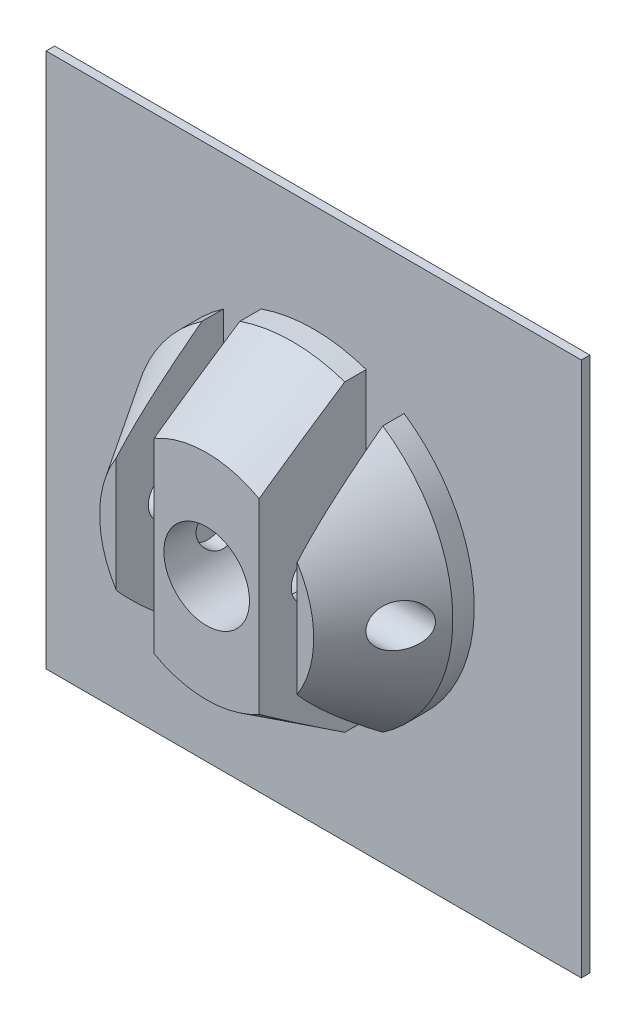
SolidWorks part; units mm, degrees
ref_plane "Alzado" through (0, 0, 0) normal (0, 0, 1) x (1, 0, 0)
ref_plane "Planta" through (0, 0, 0) normal (0, 1, 0) x (1, 0, 0)
ref_plane "Vista lateral" through (0, 0, 0) normal (1, 0, 0) x (0, 0, -1)
sketch "Croquis1" plane through (0, 0, 0) normal (0, 0, 1) x (1, 0, 0)
  line L1 (25, -25) -> (-25, -25)
  line L2 (25, -25) -> (25, 25)
  line L3 (25, 25) -> (-25, 25)
  line L4 (-25, -25) -> (-25, 25)
  line L5 (25, -25) -> (-25, 25) construction
  line L6 (25, 25) -> (-25, -25) construction
  circle A0 centre (0, 0) radius 2
  point P0 (0, 0)
  dimension "D3" = 4
  dimension "D1" = 50
  dimension "D2" = 50
extrude "Saliente-Extruir2" add sketch "Croquis1" along normal blind 0.8
ref_plane "Plano1" through (0, 0, 0) normal (1, 0, 0) x (0, 0, -1)
sketch "Croquis2" plane through (0, 0, 0) normal (1, 0, 0) x (0, 0, -1)
  line L0 (-0.8, 0) -> (-10.8, 0)
  line L1 (-0.8, 25) -> (-0.8, -25) construction
  line L2 (-10.8, 0) -> (-10.8, 10)
  line L3 (-0.8, 15) -> (-2.8, 15)
  line L4 (-0.8, 15) -> (-0.8, 0)
  line L5 (-2.8, 15) -> (-10.8, 10)
  dimension "D1" = 10
  dimension "D2" = 10
  dimension "D3" = 2
  dimension "D4" = 15
revolve "Revolución1" add sketch "Croquis2" angle 360 about L0
sketch "Croquis3" plane through (0, 0, 0.8) normal (0, 0, 1) x (1, 0, 0)
  line L2 (20, -25) -> (25, -25)
  line L3 (25, -25) -> (25, -20)
  arc A1 (20, -25) -> (25, -20) centre (25, -25) ccw
  dimension "D2" = 10
sketch "Croquis4" plane through (0, 0, 10.8) normal (0, 0, 1) x (1, 0, 0)
  line L0 (0, -0.44) -> (0, 0.44) construction
  line L1 (-8.45, 20) -> (-4.9, 20)
  line L2 (-8.45, 20) -> (-8.45, -20)
  line L3 (-8.45, -20) -> (-4.9, -20)
  line L4 (-4.9, 20) -> (-4.9, -20)
  line L5 (8.45, -20) -> (4.9, -20)
  line L6 (4.9, 20) -> (4.9, -20)
  line L7 (8.45, 20) -> (4.9, 20)
  line L8 (8.45, 20) -> (8.45, -20)
  circle A0 centre (0, 0) radius 4
  point P6 (-4.9, 0)
  dimension "D4" = 8
  dimension "D1" = 3.55
  dimension "D2" = 4.9
  dimension "D3" = 40
extrude "Cortar-Extruir1" cut sketch "Croquis4" against normal up to vertex (10 mm away) up to point (-25, 25, 0.8)
sketch "Croquis7" plane through (-25, 0, 0) normal (-1, 0, 0) x (0, 0, 1)
  line L0 (0.8, -12.3934) -> (0.8, 12.3934) construction
  circle A0 centre (5.8, 0) radius 2
  dimension "D1" = 4
  dimension "D2" = 5
extrude "Cortar-Extruir2" cut sketch "Croquis7" against normal up to vertex
extrude "Saliente-Extruir4" add sketch "Croquis3" against normal up to vertex
